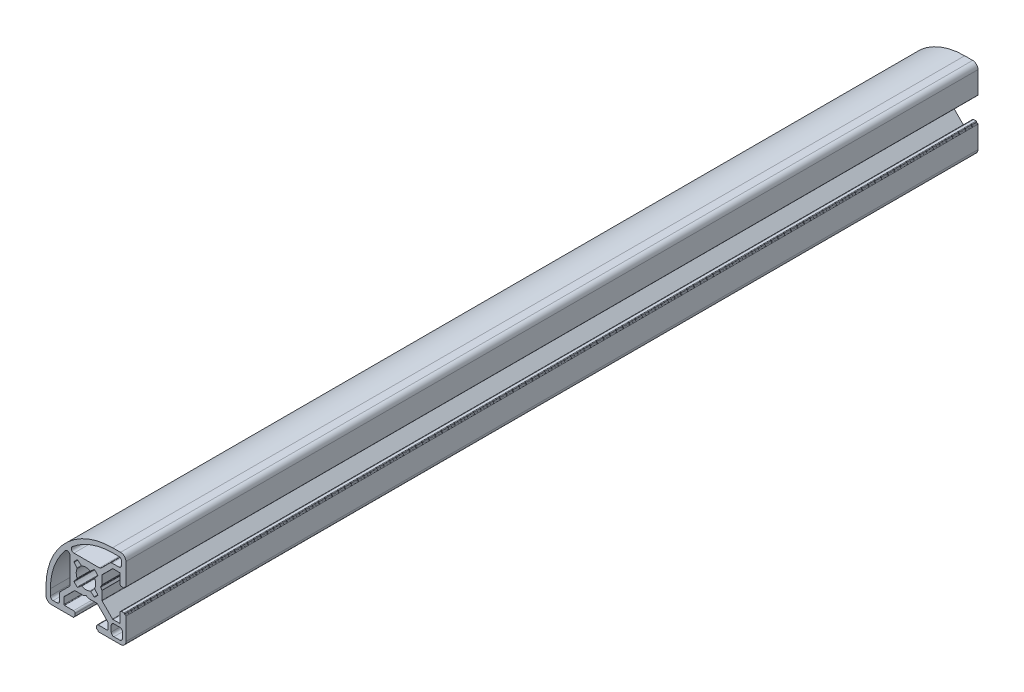
SolidWorks part; units mm, degrees
material "АД31 ГОСТ 4784-97"
ref_plane "Спереди" through (0, 0, 0) normal (0, 0, 1) x (1, 0, 0)
ref_plane "Сверху" through (0, 0, 0) normal (0, 1, 0) x (1, 0, 0)
ref_plane "Справа" through (0, 0, 0) normal (1, 0, 0) x (0, 0, -1)
sketch "Эскиз1" plane through (0, 0, 0) normal (0, 0, 1) x (1, 0, 0)
  line L0 (-5.9955, -5.0479) -> (-5.9955, 4.5146)
  line L1 (-9.6071, -9.0737) -> (-6.2884, -5.755)
  line L2 (-9.9, -12.35) -> (-9.9, -9.7808)
  line L3 (-13.35, -12.35) -> (-13.35, -10)
  line L4 (-10.9, -13.35) -> (-12.35, -13.35)
  line L5 (13.35, 10.9) -> (13.35, 12.35)
  line L6 (12.35, 13.35) -> (10, 13.35)
  line L7 (12.35, 9.9) -> (9.7808, 9.9)
  line L8 (9.0737, 9.6071) -> (5.755, 6.2884)
  line L9 (5.0479, 5.9955) -> (-4.5146, 5.9955)
  line L10 (13.7, -10.5) -> (13.7, -12.7)
  line L11 (5.9777, -0.8536) -> (5.5426, -0.1)
  line L12 (5.9777, 0.8536) -> (5.5426, 0.1)
  line L13 (6.0045, -4.1216) -> (6.0045, -0.9536)
  line L14 (6.0045, 4.1216) -> (6.0045, 0.9536)
  line L15 (-3.3344, 1.7592) -> (-4.4052, 3.0354)
  line L16 (-1.7592, 3.3344) -> (-3.0354, 4.4052)
  line L17 (1.7592, 3.3344) -> (3.0354, 4.4052)
  line L18 (3.3344, 1.7592) -> (4.4052, 3.0354)
  line L19 (15, 4.75) -> (15, 13)
  line L20 (13, 15) -> (10, 15)
  line L21 (14.5, 4.35) -> (14.5, 4.25)
  line L22 (14.3, 4.05) -> (13.4, 4.05)
  line L23 (12.8, 4.65) -> (12.8, 8.05)
  line L24 (14.7, 4.55) -> (14.8, 4.55)
  line L25 (12.6, 8.25) -> (10.1328, 8.25)
  line L26 (9.9914, 8.1914) -> (6.063, 4.263)
  line L27 (8.1914, -9.9914) -> (4.263, -6.063)
  line L28 (8.25, -12.6) -> (8.25, -10.1328)
  line L29 (9.9914, -8.1914) -> (6.063, -4.263)
  line L30 (12.6, -8.25) -> (10.1328, -8.25)
  line L31 (14.7, -4.55) -> (14.8, -4.55)
  line L32 (12.8, -4.65) -> (12.8, -8.05)
  line L33 (14.3, -4.05) -> (13.4, -4.05)
  line L34 (14.5, -4.35) -> (14.5, -4.25)
  line L35 (4.65, -12.8) -> (8.05, -12.8)
  line L36 (4.05, -14.3) -> (4.05, -13.4)
  line L37 (4.35, -14.5) -> (4.25, -14.5)
  line L38 (4.55, -14.8) -> (4.55, -14.7)
  line L39 (13, -15) -> (4.75, -15)
  line L40 (15, -4.75) -> (15, -13)
  line L41 (3.3344, -1.7592) -> (4.4052, -3.0354)
  line L42 (1.7592, -3.3344) -> (3.0354, -4.4052)
  line L43 (-1.7592, -3.3344) -> (-3.0354, -4.4052)
  line L44 (-3.3344, -1.7592) -> (-4.4052, -3.0354)
  line L45 (-15, -10) -> (-15, -13)
  line L46 (-13, -15) -> (-4.75, -15)
  line L47 (-4.55, -14.8) -> (-4.55, -14.7)
  line L48 (-4.35, -14.5) -> (-4.25, -14.5)
  line L49 (-4.05, -14.3) -> (-4.05, -13.4)
  line L50 (-4.65, -12.8) -> (-8.05, -12.8)
  line L51 (-8.1914, -9.9914) -> (-4.263, -6.063)
  line L52 (-4.1216, -6.0045) -> (-0.9536, -6.0045)
  line L53 (-0.8536, -5.9777) -> (-0.1, -5.5426)
  line L54 (12.7, -9.5) -> (10.5, -9.5)
  line L55 (9.5, -10.5) -> (9.5, -12.7)
  line L56 (10.5, -13.7) -> (12.7, -13.7)
  line L57 (0.8536, -5.9777) -> (0.1, -5.5426)
  line L58 (4.1216, -6.0045) -> (0.9536, -6.0045)
  line L59 (-8.25, -12.6) -> (-8.25, -10.1328)
  arc A0 (-5.9955, 4.5146) -> (-7.756, 5.164) centre (-6.9955, 4.5146) ccw
  arc A1 (-6.2884, -5.755) -> (-5.9955, -5.0479) centre (-6.9955, -5.0479) ccw
  arc A2 (-7.756, 5.164) -> (-13.35, -10) centre (10, -10) ccw
  arc A3 (-13.35, -12.35) -> (-12.35, -13.35) centre (-12.35, -12.35) ccw
  arc A4 (-10.9, -13.35) -> (-9.9, -12.35) centre (-10.9, -12.35) ccw
  arc A5 (-9.6071, -9.0737) -> (-9.9, -9.7808) centre (-8.9, -9.7808) ccw
  arc A6 (-5.164, 7.756) -> (-4.5146, 5.9955) centre (-4.5146, 6.9955) ccw
  arc A7 (5.0479, 5.9955) -> (5.755, 6.2884) centre (5.0479, 6.9955) ccw
  arc A8 (9.7808, 9.9) -> (9.0737, 9.6071) centre (9.7808, 8.9) ccw
  arc A9 (12.35, 9.9) -> (13.35, 10.9) centre (12.35, 10.9) ccw
  arc A10 (13.35, 12.35) -> (12.35, 13.35) centre (12.35, 12.35) ccw
  arc A11 (10, 13.35) -> (-5.164, 7.756) centre (10, -10) ccw
  arc A12 (-8.1914, -9.9914) -> (-8.25, -10.1328) centre (-8.05, -10.1328) ccw
  arc A13 (-4.1216, -6.0045) -> (-4.263, -6.063) centre (-4.1216, -6.2045) ccw
  arc A14 (-0.9536, -6.0045) -> (-0.8536, -5.9777) centre (-0.9536, -5.8045) ccw
  arc A15 (0.8536, -5.9777) -> (0.9536, -6.0045) centre (0.9536, -5.8045) ccw
  arc A16 (4.263, -6.063) -> (4.1216, -6.0045) centre (4.1216, -6.2045) ccw
  arc A17 (8.25, -10.1328) -> (8.1914, -9.9914) centre (8.05, -10.1328) ccw
  arc A18 (5.9777, 0.8536) -> (6.0045, 0.9536) centre (5.8045, 0.9536) ccw
  arc A19 (6.0045, -0.9536) -> (5.9777, -0.8536) centre (5.8045, -0.9536) ccw
  arc A20 (9.9914, -8.1914) -> (10.1328, -8.25) centre (10.1328, -8.05) ccw
  arc A21 (6.0045, -4.1216) -> (6.063, -4.263) centre (6.2045, -4.1216) ccw
  arc A22 (10.1328, 8.25) -> (9.9914, 8.1914) centre (10.1328, 8.05) ccw
  arc A23 (6.063, 4.263) -> (6.0045, 4.1216) centre (6.2045, 4.1216) ccw
  arc A24 (3.2833, 4.4125) -> (3.0354, 4.4052) centre (3.1639, 4.252) ccw
  arc A25 (4.4052, 3.0354) -> (4.4125, 3.2833) centre (4.252, 3.1639) ccw
  arc A26 (4.4125, -3.2833) -> (4.4052, -3.0354) centre (4.252, -3.1639) ccw
  arc A27 (3.0354, -4.4052) -> (3.2833, -4.4125) centre (3.1639, -4.252) ccw
  arc A28 (-3.2833, -4.4125) -> (-3.0354, -4.4052) centre (-3.1639, -4.252) ccw
  arc A29 (-4.4052, -3.0354) -> (-4.4125, -3.2833) centre (-4.252, -3.1639) ccw
  arc A30 (-4.4125, 3.2833) -> (-4.4052, 3.0354) centre (-4.252, 3.1639) ccw
  arc A31 (-3.0354, 4.4052) -> (-3.2833, 4.4125) centre (-3.1639, 4.252) ccw
  arc A32 (-3.3064, 1.5459) -> (-3.3344, 1.7592) centre (-3.4876, 1.6307) ccw
  arc A33 (-3.3344, -1.7592) -> (-3.3064, -1.5459) centre (-3.4876, -1.6307) ccw
  arc A34 (-1.5459, -3.3064) -> (-1.7592, -3.3344) centre (-1.6307, -3.4876) ccw
  arc A35 (1.7592, -3.3344) -> (1.5459, -3.3064) centre (1.6307, -3.4876) ccw
  arc A36 (3.3064, -1.5459) -> (3.3344, -1.7592) centre (3.4876, -1.6307) ccw
  arc A37 (3.3344, 1.7592) -> (3.3064, 1.5459) centre (3.4876, 1.6307) ccw
  arc A38 (1.5459, 3.3064) -> (1.7592, 3.3344) centre (1.6307, 3.4876) ccw
  arc A39 (-1.7592, 3.3344) -> (-1.5459, 3.3064) centre (-1.6307, 3.4876) ccw
  arc A40 (-1.5459, -3.3064) -> (1.5459, -3.3064) centre (0, 0) ccw
  arc A41 (-3.3064, 1.5459) -> (-3.3064, -1.5459) centre (0, 0) ccw
  arc A42 (1.5459, 3.3064) -> (-1.5459, 3.3064) centre (0, 0) ccw
  arc A43 (3.3064, -1.5459) -> (3.3064, 1.5459) centre (0, 0) ccw
  arc A44 (10, 15) -> (-15, -10) centre (10, -10) ccw
  arc A45 (5.5426, 0.1) -> (5.5426, -0.1) centre (5.7158, 0) ccw
  arc A46 (12.8, 4.65) -> (13.4, 4.05) centre (13.4, 4.65) ccw
  arc A47 (-4.05, -13.4) -> (-4.65, -12.8) centre (-4.65, -13.4) ccw
  arc A48 (4.65, -12.8) -> (4.05, -13.4) centre (4.65, -13.4) ccw
  arc A49 (13.4, -4.05) -> (12.8, -4.65) centre (13.4, -4.65) ccw
  arc A50 (-3.2833, 4.4125) -> (-4.4125, 3.2833) centre (0, 0) ccw
  arc A51 (4.4125, 3.2833) -> (3.2833, 4.4125) centre (0, 0) ccw
  arc A52 (12.8, 8.05) -> (12.6, 8.25) centre (12.6, 8.05) ccw
  arc A53 (14.7, 4.55) -> (14.5, 4.35) centre (14.7, 4.35) ccw
  arc A54 (14.3, 4.05) -> (14.5, 4.25) centre (14.3, 4.25) ccw
  arc A55 (14.8, 4.55) -> (15, 4.75) centre (14.8, 4.75) ccw
  arc A56 (15, 13) -> (13, 15) centre (13, 13) ccw
  arc A57 (13, -15) -> (15, -13) centre (13, -13) ccw
  arc A58 (15, -4.75) -> (14.8, -4.55) centre (14.8, -4.75) ccw
  arc A59 (14.5, -4.25) -> (14.3, -4.05) centre (14.3, -4.25) ccw
  arc A60 (14.5, -4.35) -> (14.7, -4.55) centre (14.7, -4.35) ccw
  arc A61 (12.6, -8.25) -> (12.8, -8.05) centre (12.6, -8.05) ccw
  arc A62 (8.05, -12.8) -> (8.25, -12.6) centre (8.05, -12.6) ccw
  arc A63 (4.05, -14.3) -> (4.25, -14.5) centre (4.25, -14.3) ccw
  arc A64 (4.55, -14.8) -> (4.75, -15) centre (4.75, -14.8) ccw
  arc A65 (4.55, -14.7) -> (4.35, -14.5) centre (4.35, -14.7) ccw
  arc A66 (3.2833, -4.4125) -> (4.4125, -3.2833) centre (0, 0) ccw
  arc A67 (-4.4125, -3.2833) -> (-3.2833, -4.4125) centre (0, 0) ccw
  arc A68 (-4.35, -14.5) -> (-4.55, -14.7) centre (-4.35, -14.7) ccw
  arc A69 (-4.75, -15) -> (-4.55, -14.8) centre (-4.75, -14.8) ccw
  arc A70 (-4.25, -14.5) -> (-4.05, -14.3) centre (-4.25, -14.3) ccw
  arc A71 (-15, -13) -> (-13, -15) centre (-13, -13) ccw
  arc A72 (9.5, -12.7) -> (10.5, -13.7) centre (10.5, -12.7) ccw
  arc A73 (10.5, -9.5) -> (9.5, -10.5) centre (10.5, -10.5) ccw
  arc A74 (13.7, -10.5) -> (12.7, -9.5) centre (12.7, -10.5) ccw
  arc A75 (12.7, -13.7) -> (13.7, -12.7) centre (12.7, -12.7) ccw
  arc A76 (0.1, -5.5426) -> (-0.1, -5.5426) centre (0, -5.7158) ccw
  arc A77 (-8.25, -12.6) -> (-8.05, -12.8) centre (-8.05, -12.6) ccw
extrude "Бобышка-Вытянуть1" add sketch "Эскиз1" along normal blind 320
